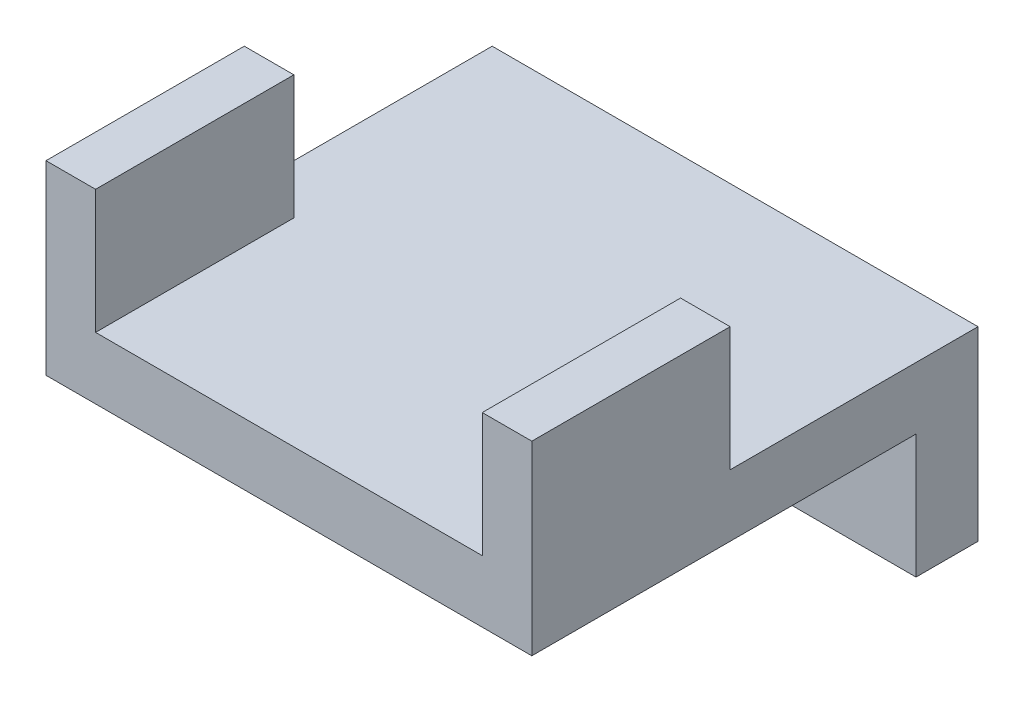
SolidWorks part; units mm, degrees
material "ABS"
ref_plane "Front Plane" through (0, 0, 0) normal (0, 0, 1) x (1, 0, 0)
ref_plane "Top Plane" through (0, 0, 0) normal (0, 1, 0) x (1, 0, 0)
ref_plane "Right Plane" through (0, 0, 0) normal (1, 0, 0) x (0, 0, -1)
sketch "Sketch2" plane through (0, 0, 0) normal (0, 1, 0) x (1, 0, 0)
  line L1 (-12.446, -11.43) -> (12.446, -11.43)
  line L2 (-12.446, -11.43) -> (-12.446, 11.43)
  line L3 (-12.446, 11.43) -> (12.446, 11.43)
  line L4 (12.446, -11.43) -> (12.446, 11.43)
  line L5 (-12.446, -11.43) -> (12.446, 11.43) construction
  line L6 (-12.446, 11.43) -> (12.446, -11.43) construction
  point P0 (0, 0)
  dimension "D1" = 22.86
  dimension "D2" = 24.892
extrude "Boss-Extrude1" add sketch "Sketch2" along normal blind 3.175
sketch "Sketch3" plane through (0, 3.175, 0) normal (0, 1, 0) x (1, 0, 0)
  line L1 (12.446, -11.43) -> (9.906, -11.43)
  line L2 (12.446, -11.43) -> (12.446, -1.27)
  line L3 (12.446, -1.27) -> (9.906, -1.27)
  line L4 (9.906, -11.43) -> (9.906, -1.27)
  line L5 (-12.446, -11.43) -> (-9.906, -11.43)
  line L6 (-12.446, -11.43) -> (-12.446, -1.27)
  line L7 (-12.446, -1.27) -> (-9.906, -1.27)
  line L8 (-9.906, -11.43) -> (-9.906, -1.27)
  dimension "D1" = 2.54
  dimension "D2" = 2.54
  dimension "D3" = 10.16
  dimension "D4" = 10.16
extrude "Boss-Extrude2" add sketch "Sketch3" along normal blind 6.35
sketch "Sketch4" plane through (0, 0, 0) normal (0, -1, 0) x (1, 0, 0)
  line L0 (-12.446, -11.43) -> (-12.446, 11.43) construction
  line L1 (12.446, -11.43) -> (-12.446, -11.43)
  line L2 (12.446, -11.43) -> (12.446, -8.255)
  line L3 (12.446, -8.255) -> (-12.446, -8.255)
  line L4 (-12.446, -11.43) -> (-12.446, -8.255)
  dimension "D1" = 3.175
extrude "Boss-Extrude3" add sketch "Sketch4" along normal blind 6.35
scale "Scale1" [suppressed]
